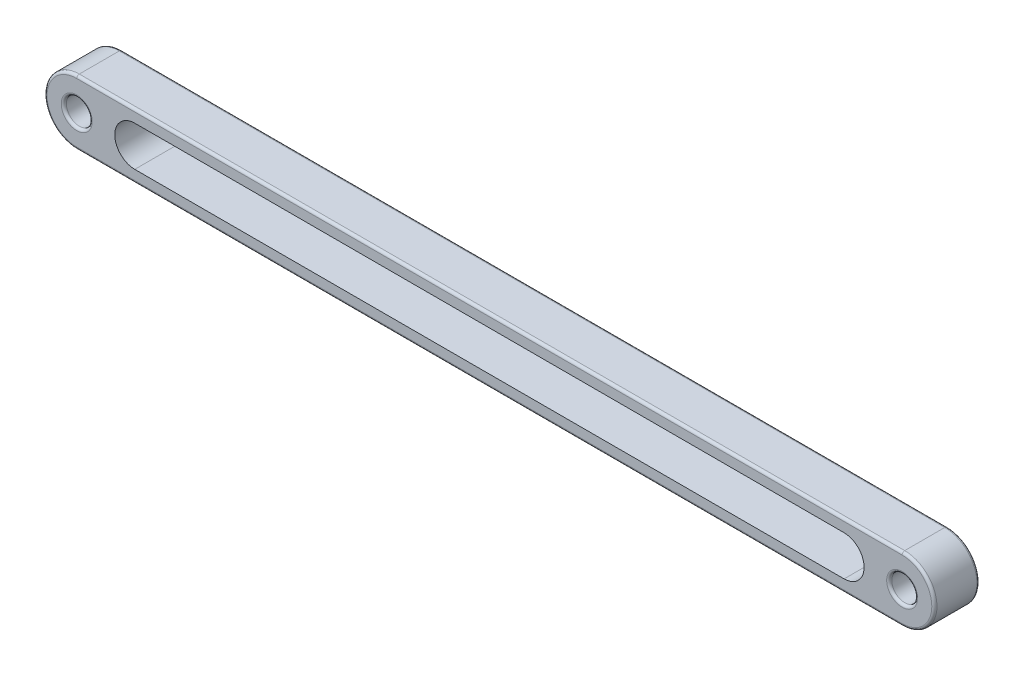
SolidWorks part; units mm, degrees
ref_plane "Front Plane" through (0, 0, 0) normal (0, 0, 1) x (1, 0, 0)
ref_plane "Top Plane" through (0, 0, 0) normal (0, 1, 0) x (1, 0, 0)
ref_plane "Right Plane" through (0, 0, 0) normal (1, 0, 0) x (0, 0, -1)
sketch "Sketch4" plane through (0, 0, 0) normal (0, 0, 1) x (1, 0, 0)
  line L0 (-320, 0) -> (320, 0) construction
  line L1 (-320, 25) -> (320, 25)
  line L2 (-320, -25) -> (320, -25)
  arc A0 (-320, 25) -> (-320, -25) centre (-320, 0) ccw
  arc A1 (320, -25) -> (320, 25) centre (320, 0) ccw
  point P3 (0, 0)
  dimension "D1" = 640
  dimension "D2" = 50
extrude "Boss-Extrude2" add sketch "Sketch4" along normal mid plane 35
sketch "Sketch5" plane through (0, 0, 17.5) normal (0, 0, 1) x (1, 0, 0)
  circle A0 centre (320, 0) radius 10
  circle A1 centre (-320, 0) radius 10
  dimension "D1" = 20
extrude "Cut-Extrude1" cut sketch "Sketch5" against normal through all
sketch "Sketch6" plane through (0, 0, -17.5) normal (0, 0, -1) x (-1, 0, 0)
  line L0 (-275, 0) -> (275, 0) construction
  line L1 (320, 0) -> (-320, 0) construction
  line L2 (-275, 15.5) -> (275, 15.5)
  line L3 (-275, -15.5) -> (275, -15.5)
  arc A0 (-275, 15.5) -> (-275, -15.5) centre (-275, 0) ccw
  arc A1 (275, -15.5) -> (275, 15.5) centre (275, 0) ccw
  point P4 (0, 0)
  dimension "D1" = 15.5
  dimension "D2" = 45
extrude "Cut-Extrude2" cut sketch "Sketch6" against normal blind 40
fillet "Fillet1" radius 2 12 edges at (345, 0, 17.5) (0, -25, 17.5) (-345, 0, 17.5) (345, 0, -17.5) (0, -25, -17.5) (-345, 0, -17.5) (0, 25, 17.5) (0, 25, -17.5) (330, 0, 17.5) (330, 0, -17.5) (-310, 0, 17.5) (-310, 0, -17.5)
